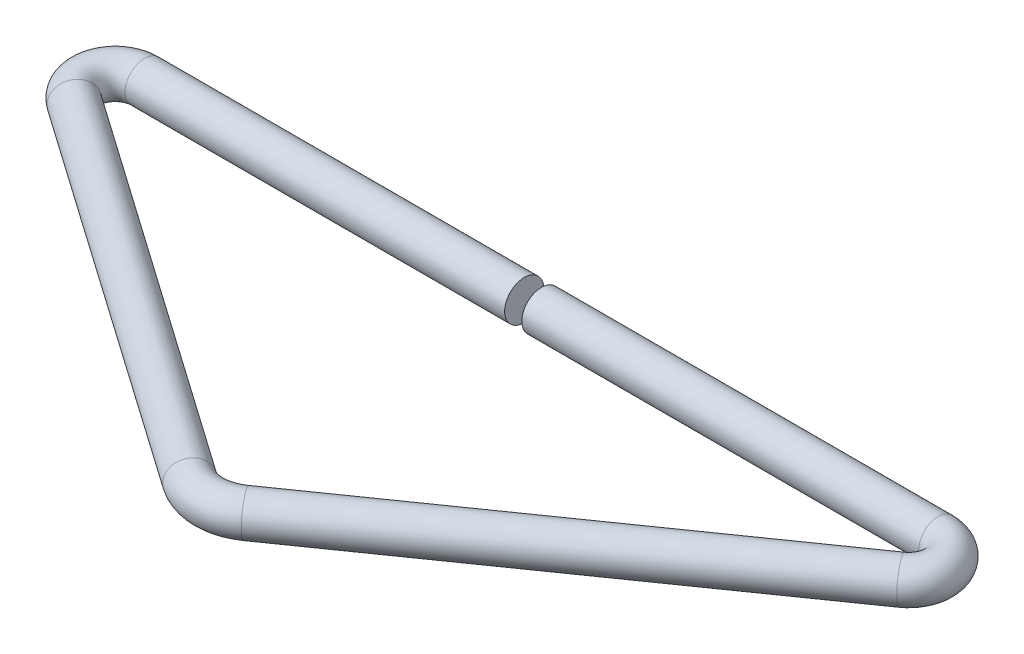
SolidWorks part; units mm, degrees
ref_plane "前视基准面" through (0, 0, 0) normal (0, 0, 1) x (1, 0, 0)
ref_plane "上视基准面" through (0, 0, 0) normal (0, 1, 0) x (1, 0, 0)
ref_plane "右视基准面" through (0, 0, 0) normal (1, 0, 0) x (0, 0, -1)
sketch "草图1" plane through (0, 0, 0) normal (0, 1, 0) x (1, 0, 0)
  line L0 (0, 0) -> (40.4852, 0)
  line L1 (42.2059, -5.4575) -> (2.8679, -33.0023)
  line L2 (-2.8679, -33.0023) -> (-42.2059, -5.4575)
  line L3 (-40.4852, 0) -> (-1.7544, 0)
  arc A0 (40.4852, 0) -> (42.2059, -5.4575) centre (40.4852, -3) cw
  arc A1 (-42.2059, -5.4575) -> (-40.4852, 0) centre (-40.4852, -3) cw
  arc A2 (2.8679, -33.0023) -> (-2.8679, -33.0023) centre (0, -28.9065) cw
  point P8 (50, 0)
  point P11 (-50, 0)
  point P14 (0, -35.0104)
  dimension "D4" = 3
  dimension "D5" = 5
  dimension "D1" = 35
  dimension "D2" = 35
  dimension "D3" = 100
sketch "草图2" plane through (0, 0, 0) normal (1, 0, 0) x (0, 0, -1)
  circle A0 centre (0, 0) radius 2
sweep "扫描2" add profiles "草图2" path "草图1"
